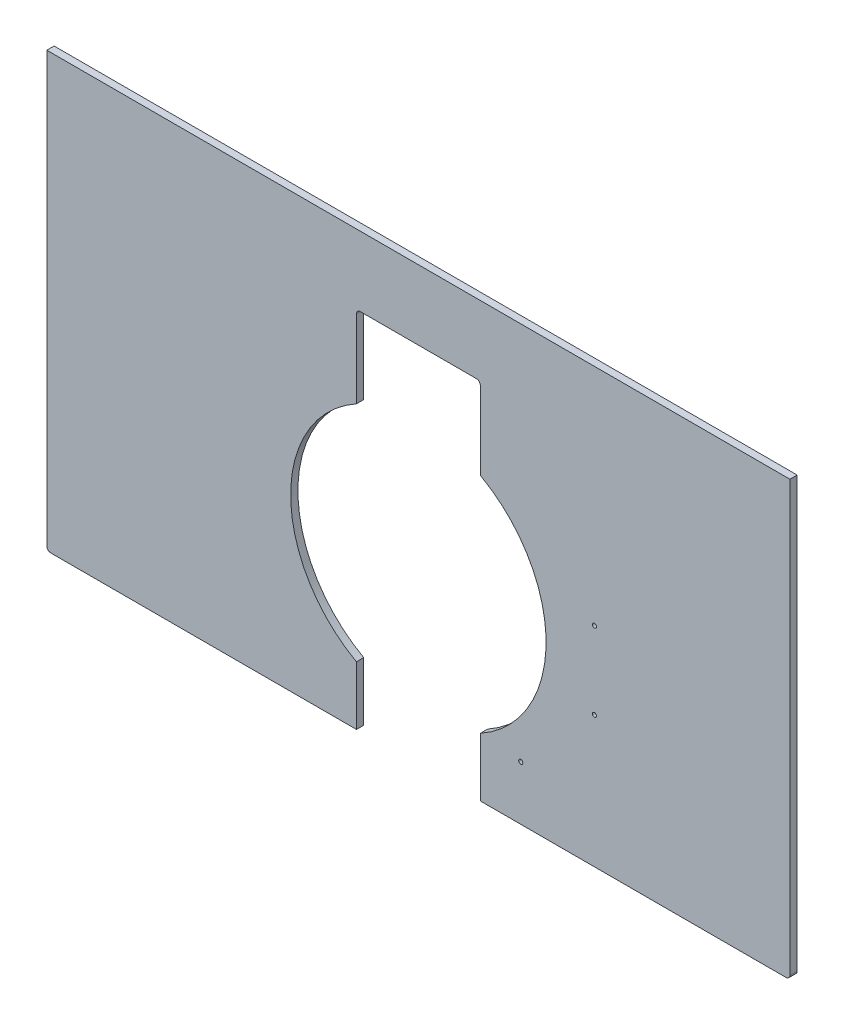
SolidWorks part; units mm, degrees
material "Pine"
ref_plane "Front Plane" through (0, 0, 0) normal (0, 0, 1) x (1, 0, 0)
ref_plane "Top Plane" through (0, 0, 0) normal (0, 1, 0) x (1, 0, 0)
ref_plane "Right Plane" through (0, 0, 0) normal (1, 0, 0) x (0, 0, -1)
sketch "Sketch1" plane through (0, 0, 0) normal (0, 0, 1) x (1, 0, 0)
  line L2 (0, 0) -> (0, 1778)
  line L3 (0, 1778) -> (1219.2, 1778)
  line L4 (1219.2, 0) -> (1219.2, 1778)
  line L5 (428.625, 736.6) -> (790.575, 736.6)
  line L6 (428.625, 736.6) -> (428.625, 1098.55)
  line L7 (428.625, 1098.55) -> (790.575, 1098.55)
  line L8 (790.575, 736.6) -> (790.575, 1098.55)
  line L15 (0, 0) -> (1219.2, 0)
  circle A1 centre (330.2, 1473.2) radius 254
  point P7 (609.6, 1098.55)
  dimension "D3" = 736.6
  dimension "D6" = 508
  dimension "D7" = 330.2
  dimension "D1" = 1219.2
  dimension "D2" = 1778
  dimension "D4" = 361.95
  dimension "D5" = 609.6
  dimension "D8" = 1473.2
extrude "Boss-Extrude1" add sketch "Sketch1" along normal blind 11.9062
sketch "Sketch3" plane through (0, 0, 11.9062) normal (0, 0, 1) x (1, 0, 0)
  line L0 (0, 0) -> (1219.2, 0) construction
  line L2 (428.625, 736.6) -> (790.575, 736.6) construction
  circle A0 centre (609.6, 279.4) radius 209.55
  point P5 (609.6, 736.6)
  dimension "D1" = 419.1
  dimension "D2" = 279.4
extrude "Cut-Extrude2" cut sketch "Sketch3" against normal through all
sketch "Sketch2" plane through (0, 0, 11.9062) normal (0, 0, 1) x (1, 0, 0)
  line L1 (508, 127) -> (711.2, 127)
  line L2 (508, 127) -> (508, -38.1)
  line L3 (508, -38.1) -> (711.2, -38.1)
  line L4 (711.2, 127) -> (711.2, -38.1)
  line L6 (508, 596.9) -> (711.2, 596.9)
  line L7 (508, 596.9) -> (508, 431.8)
  line L8 (508, 431.8) -> (711.2, 431.8)
  line L9 (711.2, 596.9) -> (711.2, 431.8)
  line L10 (790.575, 1098.55) -> (428.625, 1098.55) construction
  circle A0 centre (609.6, 279.4) radius 241.3 construction
  point P12 (609.6, 596.9)
  point P15 (609.6, 1098.55)
  point P16 (609.6, -38.1)
  point P17 (609.6, 431.8)
  dimension "D3" = 482.6
  dimension "D4" = 165.1
  dimension "D2" = 317.5
  dimension "D5" = 317.5
  dimension "D1" = 203.2
  dimension "D6" = 165.1
extrude "Cut-Extrude1" cut sketch "Sketch2" against normal through all
sketch "Sketch4" plane through (0, 0, 11.9062) normal (0, 0, 1) x (1, 0, 0)
  line L1 (0, 0) -> (508, 0) construction
  line L6 (0, 1778) -> (0, 0) construction
  circle A0 centre (50.8, 12.7) radius 3.3655
  dimension "D1" = 6.731
  dimension "D2" = 12.7
  dimension "D3" = 50.8
extrude "Cut-Extrude3" [suppressed] cut sketch "Sketch4" against normal through all
pattern_linear "LPattern1" [suppressed] count 5 spacing 425.45
sketch "Sketch5" plane through (0, 0, 11.9062) normal (0, 0, 1) x (1, 0, 0)
  line L0 (1219.2, 1778) -> (0, 1778) construction
  line L1 (0, 1778) -> (0, 0) construction
  circle A0 centre (609.6, 1714.5) radius 3.429
  dimension "D1" = 63.5
  dimension "D2" = 6.858
  dimension "D3" = 609.6
extrude "Cut-Extrude4" cut sketch "Sketch5" against normal through all
pattern_linear "LPattern2" count 3 spacing 301.625 along (0, -1, 0) of "Cut-Extrude4"
sketch "Sketch6" plane through (0, 0, 11.9062) normal (0, 0, 1) x (1, 0, 0)
  line L0 (0, 0) -> (508, 0) construction
  line L2 (0, 1778) -> (0, 0) construction
  circle A0 centre (127, 12.7) radius 3.3782
  circle A1 centre (381, 12.7) radius 3.3782
  dimension "D1" = 12.7
  dimension "D3" = 6.7564
  dimension "D2" = 254
  dimension "D4" = 127
extrude "Cut-Extrude5" [suppressed] cut sketch "Sketch6" against normal through all
sketch "Sketch7" plane through (0, 0, 11.9062) normal (0, 0, 1) x (1, 0, 0)
  line L1 (711.2, 0) -> (1219.2, 0) construction
  circle A0 centre (777.6052, 88.9) radius 3.3782
  circle A1 centre (609.6, 279.4) radius 241.3 construction
  circle A2 centre (777.6052, 88.9) radius 12.7 construction
  circle A3 centre (609.6, 279.4) radius 254 construction
  circle A4 centre (898.525, 342.9) radius 3.3782
  circle A5 centre (898.525, 215.9) radius 3.3782
  dimension "D1" = 63.5
  dimension "D3" = 6.7564
  dimension "D4" = 482.6
  dimension "D5" = 25.4
  dimension "D6" = 508
  dimension "D2" = 88.9
  dimension "D7" = 127
  dimension "D12" = 288.925
  dimension "D13" = 215.9
extrude "Cut-Extrude6" cut sketch "Sketch7" against normal through all contours A4 | A5 | A0
sketch "Sketch9" plane through (0, 0, 11.9062) normal (0, 0, 1) x (1, 0, 0)
  line L0 (0, 0) -> (508, 0) construction
  line L1 (0, 1778) -> (0, 0) construction
  point P0 (127, 85.725)
  point P1 (190.5, 85.725)
  dimension "D1" = 63.5
  dimension "D2" = 85.725
  dimension "D3" = 127
hole_wizard "CSK for 1/4 Flat Head Machine Screw1" [suppressed] positions "Sketch10" profile "Sketch11" countersink size "1/4" standard "ANSI Inch"
sketch "Sketch10" plane through (0, 0, 6.35) normal (0, 0, 1) x (1, 0, 0)
  point P0 (127, 85.725)
  point P3 (190.5, 85.725)
sketch "Sketch11" plane through (127, 85.725, 6.35) normal (1, 0, 0) x (0, -1, 0)
  line L0 (0, 0) -> (0, 6.35)
  line L1 (0, 6.35) -> (3.5712, 6.35)
  line L2 (3.5712, 6.35) -> (3.5712, 3.2989)
  line L3 (3.5712, 3.2989) -> (6.4389, 0)
  line L5 (6.4389, 0) -> (0, 0)
  line L6 (-3.5712, 3.2989) -> (-6.4389, 0) construction
  line L11 (0, -6.35) -> (0, 107.95) construction
  dimension "Thru Hole Dia." = 7.1425
  dimension "Thru Hole Depth" = 6.35
  dimension "Near C'Sink Dia." = 12.8778
  dimension "Near C'Sink Angle" = 82
pattern_linear "LPattern3" [suppressed] count 2 spacing 901.7
sketch "Sketch12" plane through (0, 0, 11.9062) normal (0, 0, 1) x (1, 0, 0)
  line L0 (0, 1778) -> (0, 0) construction
  line L1 (1219.2, 0) -> (1219.2, 1778) construction
  line L2 (1219.2, 1778) -> (0, 1778) construction
  circle A0 centre (203.2, 1727.2) radius 4.7625
  circle A1 centre (1016, 1727.2) radius 4.7625
  dimension "D1" = 203.2
  dimension "D4" = 9.525
  dimension "D2" = 203.2
  dimension "D3" = 50.8
extrude "Cut-Extrude7" cut sketch "Sketch12" against normal through all
ref_plane "Plane1" through (609.6, 0, 0) normal (-1, 0, 0) x (0, 0, 1)
sketch "Sketch14" plane through (0, 0, 11.9062) normal (0, 0, 1) x (1, 0, 0)
  line L0 (0, 1778) -> (0, 0) construction
  line L1 (1219.2, 1778) -> (0, 1778) construction
  line L2 (0, 0) -> (508, 0) construction
  circle A0 centre (31.75, 1651) radius 4.7625
  circle A1 centre (31.75, 914.4) radius 4.7625
  circle A2 centre (31.75, 304.8) radius 4.7625
  dimension "D1" = 31.75
  dimension "D2" = 9.525
  dimension "D3" = 127
  dimension "D4" = 304.8
  dimension "D5" = 914.4
extrude "Cut-Extrude8" [suppressed] cut sketch "Sketch14" against normal through all
mirror "Mirror1" [suppressed] about plane through (609.6, 0, 0) normal (-1, 0, 0)
sketch "Sketch15" plane through (0, 0, 11.9062) normal (0, 0, 1) x (1, 0, 0)
  line L0 (428.625, 736.6) -> (790.575, 736.6) construction
  line L1 (428.625, 1098.55) -> (428.625, 736.6) construction
  circle A0 centre (403.225, 736.6) radius 4.7625
  circle A1 centre (403.225, 682.625) radius 4.7625
  dimension "D1" = 53.975
  dimension "D3" = 9.525
  dimension "D2" = 25.4
extrude "Cut-Extrude9" [suppressed] cut sketch "Sketch15" against normal through all
mirror "Mirror2" [suppressed] about plane through (609.6, 0, 0) normal (-1, 0, 0)
sketch "Sketch16" plane through (0, 0, 11.9062) normal (0, 0, 1) x (1, 0, 0)
  line L0 (428.625, 1098.55) -> (428.625, 736.6) construction
  line L1 (428.625, 736.6) -> (790.575, 736.6) construction
  line L2 (790.575, 736.6) -> (790.575, 1098.55) construction
  circle A0 centre (419.1, 1054.1) radius 4.7625
  circle A1 centre (419.1, 787.4) radius 4.7625
  circle A2 centre (800.1, 1054.1) radius 4.7625
  circle A3 centre (800.1, 787.4) radius 4.7625
  dimension "D1" = 9.525
  dimension "D2" = 9.525
  dimension "D3" = 266.7
  dimension "D4" = 50.8
  dimension "D5" = 9.525
extrude "Cut-Extrude10" cut sketch "Sketch16" against normal through all
fillet "Fillet1" [suppressed] radius 12.7
fillet "Fillet2" radius 6.35 8 edges at (508, 596.9, 5.9531) (711.2, 596.9, 5.9531) (790.575, 736.6, 5.9531) (790.575, 1098.55, 5.9531) (428.625, 1098.55, 5.9531) (428.625, 736.6, 5.9531) (0, 0, 5.9531) (1219.2, 0, 5.9531)
sketch "Sketch17" plane through (0, 0, 11.9062) normal (0, 0, 1) x (1, 0, 0)
  line L0 (44.45, 0) -> (463.55, 0) construction
  line L1 (0, 1778) -> (0, 6.35) construction
  circle A4 centre (416.5676, 76.2) radius 3.937
  circle A5 centre (416.5676, 19.05) radius 3.937
  circle A6 centre (797.5676, 19.05) radius 3.937
  circle A7 centre (797.5676, 76.2) radius 3.937
  dimension "D3" = 381
  dimension "D4" = 19.05
  dimension "D1" = 7.874
  dimension "D2" = 57.15
  dimension "D5" = 416.5676
extrude "Cut-Extrude11" [suppressed] cut sketch "Sketch17" against normal through all
sketch "Sketch18" plane through (0, 0, 11.9062) normal (0, 0, 1) x (1, 0, 0)
  line L0 (0, 1778) -> (0, 6.35) construction
  line L1 (711.2, 0) -> (1212.85, 0) construction
  circle A0 centre (418.1551, 576.972) radius 3.9687
  circle A1 centre (418.1551, 481.722) radius 3.9687
  circle A2 centre (799.1551, 481.722) radius 3.9687
  circle A3 centre (799.1551, 576.972) radius 3.9687
  dimension "D2" = 7.9375
  dimension "D1" = 95.25
  dimension "D3" = 381
  dimension "D4" = 418.1551
  dimension "D5" = 481.722
extrude "Cut-Extrude12" [suppressed] cut sketch "Sketch18" against normal through all
sketch "Sketch19" plane through (0, 0, 11.9062) normal (0, 0, 1) x (1, 0, 0)
  line L0 (0, 711.2) -> (1219.2, 711.2)
  line L1 (0, 1778) -> (0, 6.35) construction
  line L2 (1219.2, 6.35) -> (1219.2, 1778) construction
  line L3 (6.35, 0) -> (508, 0) construction
  line L6 (0, 711.2) -> (0, 1778)
  line L7 (0, 1778) -> (1219.2, 1778)
  line L8 (1219.2, 711.2) -> (1219.2, 1778)
  dimension "D1" = 711.2
extrude "Cut-Extrude13" cut sketch "Sketch19" against normal blind 12.7
sketch "Sketch20" [suppressed] plane through (0, 0, 11.9062) normal (0, 0, 1) x (1, 0, 0)
  line L0 (609.6, 711.2) -> (609.6, 0) construction
  line L1 (0, 711.2) -> (1219.2, 711.2) construction
  line L2 (1219.2, 6.35) -> (1219.2, 711.2) construction
  line L3 (723.9, 0) -> (1212.85, 0) construction
  circle A0 centre (777.6052, 88.9) radius 3.175
  circle A2 centre (898.525, 215.9) radius 3.4279
  circle A3 centre (898.525, 342.9) radius 3.3782
  circle A4 centre (320.675, 342.9) radius 3.3782
  circle A5 centre (320.675, 215.9) radius 3.4279
  circle A7 centre (860.806, 166.116) radius 3.175
  circle A8 centre (358.394, 166.116) radius 3.175
  circle A9 centre (448.31, 76.2) radius 3.175
  dimension "D1" = 6.35
  dimension "D4" = 6.35
  dimension "D5" = 358.394
  dimension "D6" = 166.116
extrude "Cut-Extrude14" [suppressed] cut sketch "Sketch20" against normal through all
